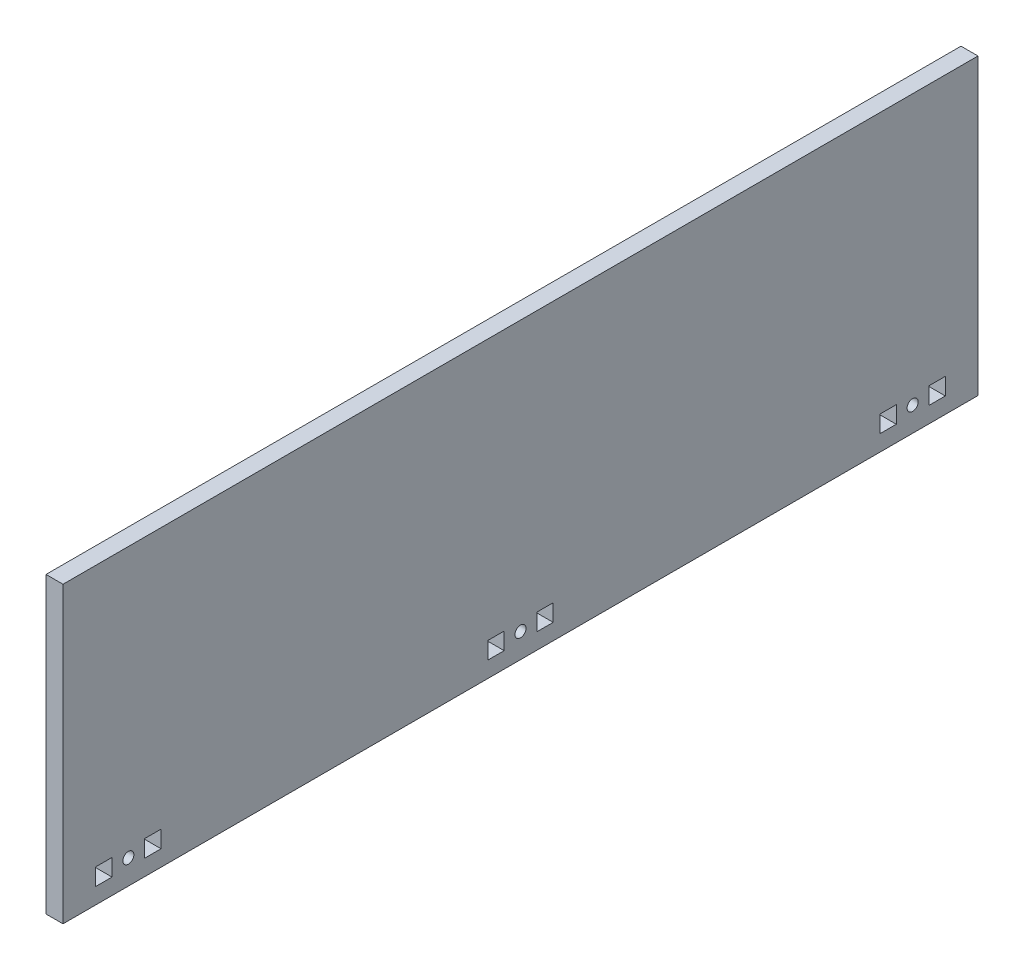
SolidWorks part; units mm, degrees
material "Acrylic (Blue)"
ref_plane "Front Plane" through (0, 0, 0) normal (0, 0, 1) x (1, 0, 0)
ref_plane "Top Plane" through (0, 0, 0) normal (0, 1, 0) x (1, 0, 0)
ref_plane "Right Plane" through (0, 0, 0) normal (1, 0, 0) x (0, 0, -1)
sketch "Sketch1" plane through (0, 0, 0) normal (1, 0, 0) x (0, 0, -1)
  line L0 (-139.7, 12.827) -> (-12.7, 12.827) construction
  line L1 (-177.8, 114.3) -> (177.8, 114.3)
  line L2 (-177.8, 114.3) -> (-177.8, 0)
  line L3 (-177.8, 0) -> (177.8, 0)
  line L4 (177.8, 114.3) -> (177.8, 0)
  line L5 (12.7, 12.827) -> (139.7, 12.827) construction
  line B0 (-146.05, 12.827) -> (-139.7, 12.827)
  line B1 (-139.7, 12.827) -> (-139.7, 6.223)
  line B2 (-139.7, 6.223) -> (-146.05, 6.223)
  line B3 (-146.05, 6.223) -> (-146.05, 12.827)
  line B4 (-165.1, 12.827) -> (-158.75, 12.827)
  line B5 (-158.75, 12.827) -> (-158.75, 6.223)
  line B6 (-158.75, 6.223) -> (-165.1, 6.223)
  line B7 (-165.1, 6.223) -> (-165.1, 12.827)
  circle B8 centre (-152.4, 9.525) radius 2.1526
  line B9 (6.35, 12.827) -> (12.7, 12.827)
  line B10 (12.7, 12.827) -> (12.7, 6.223)
  line B11 (12.7, 6.223) -> (6.35, 6.223)
  line B12 (6.35, 6.223) -> (6.35, 12.827)
  line B13 (-12.7, 12.827) -> (-6.35, 12.827)
  line B14 (-6.35, 12.827) -> (-6.35, 6.223)
  line B15 (-6.35, 6.223) -> (-12.7, 6.223)
  line B16 (-12.7, 6.223) -> (-12.7, 12.827)
  circle B17 centre (0, 9.525) radius 2.1526
  line B18 (158.75, 12.827) -> (165.1, 12.827)
  line B19 (165.1, 12.827) -> (165.1, 6.223)
  line B20 (165.1, 6.223) -> (158.75, 6.223)
  line B21 (158.75, 6.223) -> (158.75, 12.827)
  line B22 (139.7, 12.827) -> (146.05, 12.827)
  line B23 (146.05, 12.827) -> (146.05, 6.223)
  line B24 (146.05, 6.223) -> (139.7, 6.223)
  line B25 (139.7, 6.223) -> (139.7, 12.827)
  circle B26 centre (152.4, 9.525) radius 2.1526
  dimension "D1" = 114.3
  dimension "D2" = 355.6
  dimension "D3" = 12.7
  dimension "D4" = 12.7
  dimension "D5" = 9.525
sketch_block_instance "BOLT_HOLE-1"
sketch_block "BOLT_HOLE" parameters "D1"=4.3053, "D2"=6.35, "D3"=6.35, "D4"=6.604
sketch_block_instance "BOLT_HOLE-2"
sketch_block_instance "BOLT_HOLE-3"
extrude "Boss-Extrude1" add sketch "Sketch1" along normal blind 6.604
